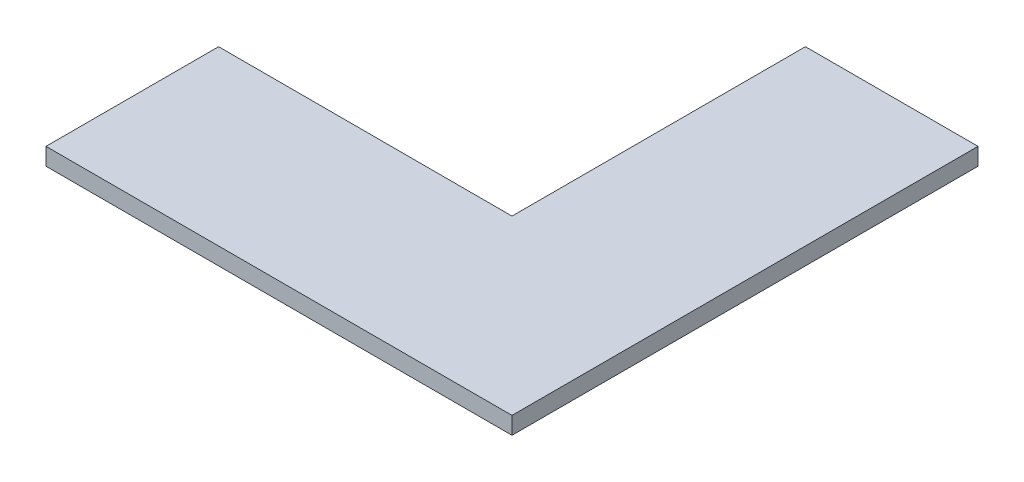
SolidWorks part; units mm, degrees
ref_plane "Front Plane" through (0, 0, 0) normal (0, 0, 1) x (1, 0, 0)
ref_plane "Top Plane" through (0, 0, 0) normal (0, 1, 0) x (1, 0, 0)
ref_plane "Right Plane" through (0, 0, 0) normal (1, 0, 0) x (0, 0, -1)
sketch "Sketch1" plane through (0, 0, 0) normal (0, 1, 0) x (1, 0, 0)
  line L0 (-135, 135) -> (135, -135) construction
  line L1 (-135, 135) -> (135, 135) construction
  line L2 (-135, 135) -> (-135, -135) construction
  line L3 (-135, -135) -> (135, -135) construction
  line L4 (135, 135) -> (135, -135) construction
  line L5 (-135, -135) -> (135, -135)
  line L6 (135, -135) -> (135, 135)
  line L7 (135, 135) -> (35, 135)
  line L8 (35, 135) -> (35, -35)
  line L9 (35, -35) -> (-135, -35)
  line L10 (-135, -35) -> (-135, -135)
  dimension "D1" = 270
  dimension "D2" = 270
  dimension "D3" = 100
  dimension "D4" = 100
extrude "Boss-Extrude1" add sketch "Sketch1" along normal blind 10
